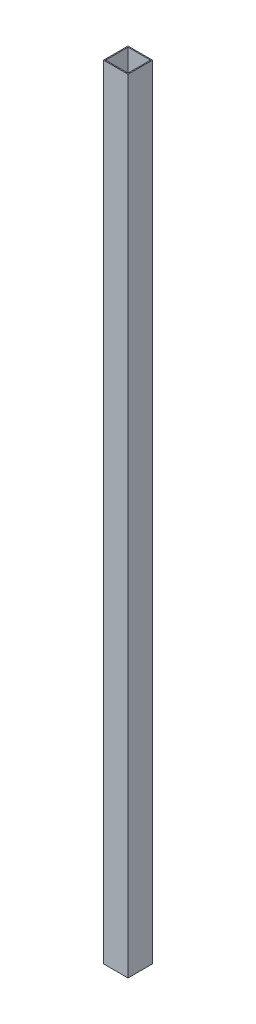
SolidWorks part; units mm, degrees
material "Galvanized Steel"
ref_plane "Front Plane" through (0, 0, 0) normal (0, 0, 1) x (1, 0, 0)
ref_plane "Top Plane" through (0, 0, 0) normal (0, 1, 0) x (1, 0, 0)
ref_plane "Right Plane" through (0, 0, 0) normal (1, 0, 0) x (0, 0, -1)
sketch "Sketch1" plane through (0, 0, 0) normal (0, 1, 0) x (1, 0, 0)
  line L1 (-38.1, 38.1) -> (38.1, 38.1)
  line L2 (-38.1, 38.1) -> (-38.1, -38.1)
  line L3 (-38.1, -38.1) -> (38.1, -38.1)
  line L4 (38.1, 38.1) -> (38.1, -38.1)
  line L5 (-38.1, 38.1) -> (38.1, -38.1) construction
  line L6 (-38.1, -38.1) -> (38.1, 38.1) construction
  line L7 (-35.052, 35.052) -> (35.052, 35.052)
  line L8 (-35.052, 35.052) -> (-35.052, -35.052)
  line L9 (-35.052, -35.052) -> (35.052, -35.052)
  line L10 (35.052, 35.052) -> (35.052, -35.052)
  line L11 (-35.052, 35.052) -> (35.052, -35.052) construction
  line L12 (-35.052, -35.052) -> (35.052, 35.052) construction
  point P0 (0, 0)
  point P6 (0, 0)
  dimension "D1" = 76.2
  dimension "D2" = 70.104
extrude "Boss-Extrude1" add sketch "Sketch1" along normal blind 2438.4
